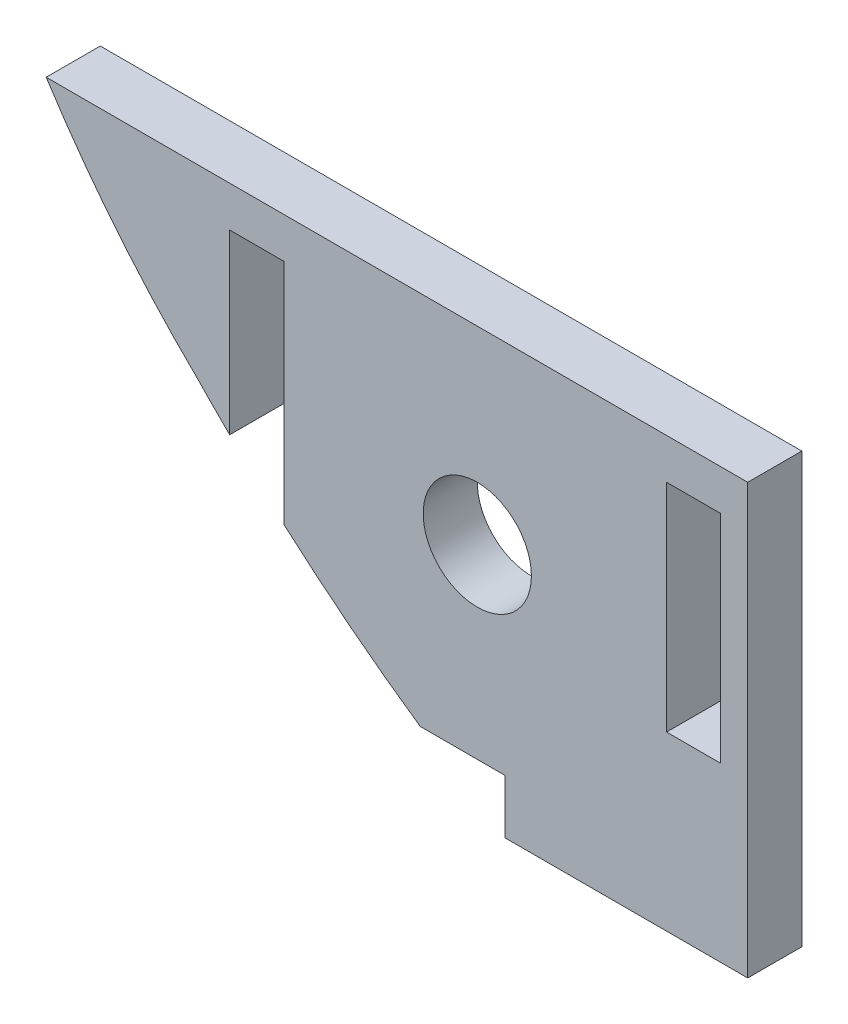
SolidWorks part; units mm, degrees
ref_plane "Front Plane" through (0, 0, 0) normal (0, 0, 1) x (1, 0, 0)
ref_plane "Top Plane" through (0, 0, 0) normal (0, 1, 0) x (1, 0, 0)
ref_plane "Right Plane" through (0, 0, 0) normal (1, 0, 0) x (0, 0, -1)
sketch "Sketch1" plane through (0, 0, 0) normal (0, 0, 1) x (1, 0, 0)
  line L0 (-6.6541, -12.7061) -> (-6.6541, -10.7061)
  line L1 (-23.6167, 3.1696) -> (2.3245, 3.1696)
  line L2 (-9.7836, -10.7061) -> (-6.6541, -10.7061)
  line L3 (1.3245, 1.6696) -> (1.3245, -6.3304)
  line L4 (1.3245, -6.3304) -> (-0.6755, -6.3304)
  line L5 (2.3245, 3.1696) -> (2.3245, -12.7061)
  line L6 (-0.6755, -6.3304) -> (-0.6755, 1.6696)
  line L7 (-0.6755, 1.6696) -> (1.3245, 1.6696)
  line L8 (-6.6541, -12.7061) -> (2.3245, -12.7061)
  line L14 (-14.8318, 1.6696) -> (-14.8318, -6.7543)
  line L19 (-16.8318, -4.8895) -> (-16.8318, 1.6696)
  line L22 (-16.8318, 1.6696) -> (-14.8318, 1.6696)
  arc A0 (-23.6167, 3.1696) -> (-18, -3.7061) centre (8.865, 23.9719) ccw
  arc A1 (-18, -3.7061) -> (-16.8318, -4.8895) centre (20.321, 32.9518) ccw
  circle A2 centre (-7.6755, -3.8304) radius 2
  arc A3 (-14.8318, -6.7543) -> (-9.7836, -10.7061) centre (20.321, 32.9518) ccw
  dimension "D1" = 4
  dimension "D2" = 38.572
  dimension "D3" = 53.0311
  dimension "D4" = 1.3245
  dimension "D5" = 2.3245
  dimension "D6" = 8.865
  dimension "D7" = 20.321
  dimension "D8" = 6.6541
  dimension "D9" = 7.6755
  dimension "D10" = 14.8318
  dimension "D11" = 1.6696
  dimension "D12" = 3.1696
  dimension "D13" = 3.8304
  dimension "D14" = 18
  dimension "D15" = 23.6167
  dimension "D16" = 6.3304
extrude "Boss-Extrude1" add sketch "Sketch1" along normal blind 2
